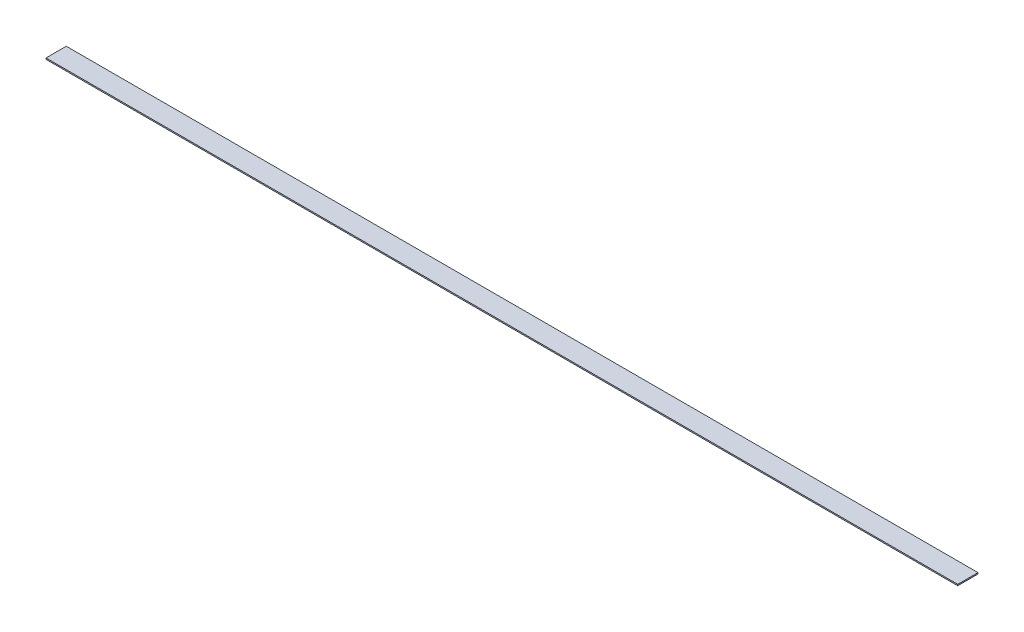
SolidWorks part; units mm, degrees
material "Nylon 101"
ref_plane "Front Plane" through (0, 0, 0) normal (0, 0, 1) x (1, 0, 0)
ref_plane "Top Plane" through (0, 0, 0) normal (0, 1, 0) x (1, 0, 0)
ref_plane "Right Plane" through (0, 0, 0) normal (1, 0, 0) x (0, 0, -1)
sketch "Sketch1" plane through (0, 0, 0) normal (0, 1, 0) x (1, 0, 0)
  line L1 (0, 0) -> (1143, 0)
  line L2 (0, 0) -> (0, 25.4)
  line L3 (0, 25.4) -> (1143, 25.4)
  line L4 (1143, 0) -> (1143, 25.4)
  dimension "D1" = 25.4
  dimension "D2" = 1143
extrude "Boss-Extrude1" add sketch "Sketch1" along normal blind 1.5875
